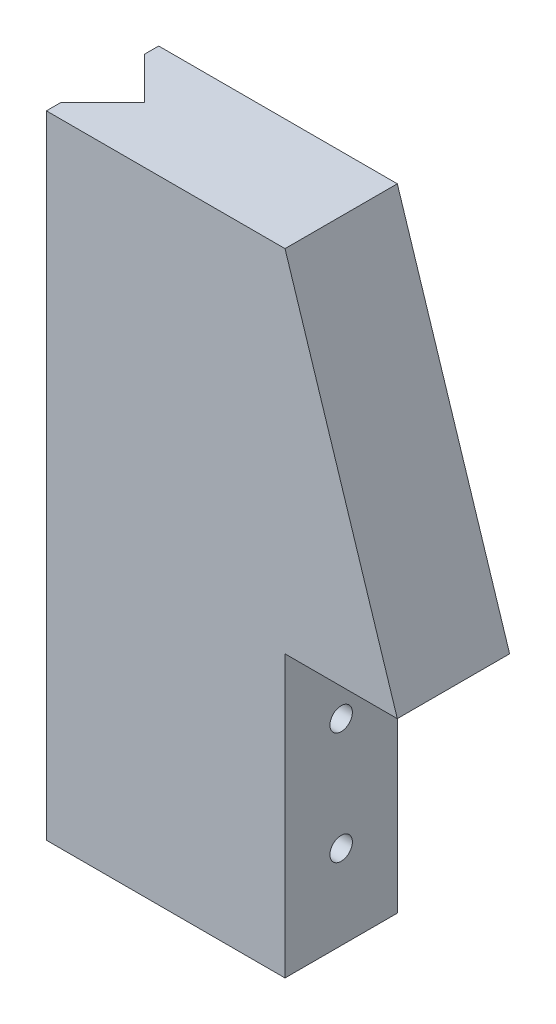
SolidWorks part; units mm, degrees
ref_plane "正面" through (0, 0, 0) normal (0, 0, 1) x (1, 0, 0)
ref_plane "平面" through (0, 0, 0) normal (0, 1, 0) x (1, 0, 0)
ref_plane "右側面" through (0, 0, 0) normal (1, 0, 0) x (0, 0, -1)
sketch "Sketch1" plane through (0, 0, 0) normal (0, 0, 1) x (1, 0, 0)
  line L0 (0, 0) -> (-8, 0)
  line L1 (-8, 0) -> (-8, -20)
  line L2 (-8, -20) -> (-25, -20)
  line L3 (-25, -20) -> (-25, 25)
  line L4 (-25, 25) -> (-8, 25)
  line L5 (-8, 25) -> (0, 0)
  dimension "D1" = 20
  dimension "D2" = 45
extrude "Boss-Extrude1" add sketch "Sketch1" along normal blind 8
sketch "Sketch2" plane through (0, 25, 0) normal (0, 1, 0) x (1, 0, 0)
  line L0 (-25, -4) -> (-25, -1)
  line L1 (-25, -8) -> (-25, 0) construction
  line L5 (-25, -4) -> (-25, -7)
  line L7 (-25, -7) -> (-22, -4)
  line L8 (-22, -4) -> (-25, -1)
extrude "Cut-Extrude1" cut sketch "Sketch2" against normal through all
hole_wizard "M2x0.4 Tapped Hole1" positions "3DSketch1" profile "Sketch3" tap size "M2x0.4" standard "JIS"
sketch3d "3DSketch1"
  line L0 (-8, -20, 8) -> (-8, 0, 8) construction
  line L3 (-8, 0, 8) -> (-8, 0, 0) construction
  point P0 (-8, -6, 4)
  point P2 (-8, -14, 4)
  dimension "D1" = 4
  dimension "D2" = 6
  dimension "D3" = 14
  dimension "D4" = 4
cosmetic thread "Hole Thread1" parameters "D1"=4.6, "D2"=2
cosmetic thread "Hole Thread2" parameters "D1"=4.6, "D2"=2
sketch "Sketch3" plane through (-8, -6, 4) normal (0, 1, 0) x (0, 0, -1)
  line L0 (0, 0) -> (0, 5.4807)
  line L1 (0, 5.4807) -> (0.8, 5)
  line L2 (0.8, 5) -> (0.8, 0)
  line L5 (0.8, 0) -> (0, 0)
  line L10 (0, 5.4807) -> (-0.8, 5) construction
  line L11 (0, -6.35) -> (0, 107.95) construction
  dimension "Tap Drill Dia." = 1.6
  dimension "Tap Drill Depth" = 5
  dimension "Drill Angle" = 118
